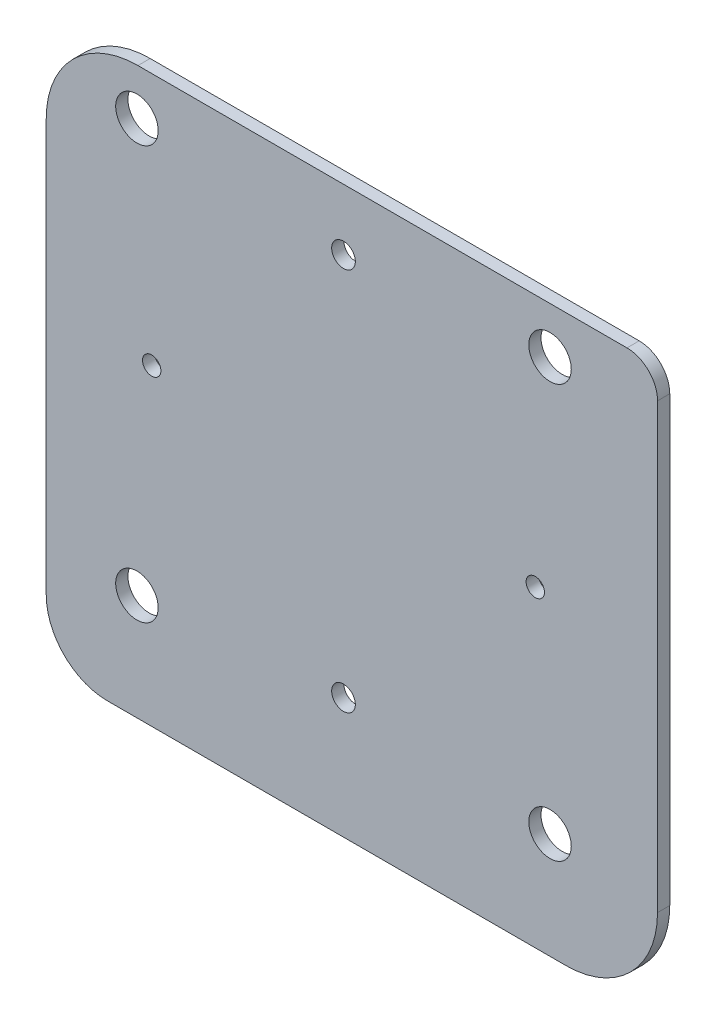
SolidWorks part; units mm, degrees
material "FR4_stuffedProtoboard"
ref_plane "Front Plane" through (0, 0, 0) normal (0, 0, 1) x (1, 0, 0)
ref_plane "Top Plane" through (0, 0, 0) normal (0, 1, 0) x (1, 0, 0)
ref_plane "Right Plane" through (0, 0, 0) normal (1, 0, 0) x (0, 0, -1)
sketch "Imported DXF" plane through (0, 0, 0) normal (0, 0, 1) x (1, 0, 0)
  line L0 (-21.6929, 33.1) -> (40.8929, 33.1)
  line L1 (41.2464, 32.9535) -> (43.9536, 30.2464)
  line L2 (44.1, 29.8929) -> (44.1, -26.6929)
  line L3 (43.9535, -27.0465) -> (30.2464, -40.7536)
  line L4 (29.8929, -40.9) -> (-30.6929, -40.9)
  line L5 (-31.0465, -40.7536) -> (-38.7536, -33.0464)
  line L6 (-38.9001, -32.6946) -> (-38.9148, 15.8797)
  line L7 (-38.7685, 16.2316) -> (-22.0464, 32.9536)
  line L8 (34.175, 6.26) -> (32.925, 6.26)
  line L9 (32.925, 6.26) -> (32.925, 8.26)
  line L10 (32.925, 8.26) -> (34.175, 8.26)
  line L11 (34.175, 8.26) -> (34.175, 6.26)
  line L12 (5.75, 8.485) -> (5.75, 9.735)
  line L13 (5.75, 9.735) -> (7.75, 9.735)
  line L14 (7.75, 9.735) -> (7.75, 8.485)
  line L15 (7.75, 8.485) -> (5.75, 8.485)
  line L16 (-4.91, -8.495) -> (-4.91, -9.745)
  line L17 (-4.91, -9.745) -> (-6.91, -9.745)
  line L18 (-6.91, -9.745) -> (-6.91, -8.495)
  line L19 (-6.91, -8.495) -> (-4.91, -8.495)
  line L20 (39.91, -3.075) -> (32.29, -3.075)
  line L21 (32.29, 3.275) -> (39.91, 3.275)
  line L22 (32.671, -3.075) -> (32.29, -3.075)
  line L23 (32.29, -3.075) -> (32.29, 3.275)
  line L24 (32.29, 3.275) -> (32.671, 3.275)
  line L25 (39.529, -3.075) -> (39.91, -3.075)
  line L26 (39.91, -3.075) -> (39.91, 3.275)
  line L27 (39.91, 3.275) -> (39.529, 3.275)
  line L28 (-3.81, 15.275) -> (3.81, 15.275)
  line L29 (3.81, 8.925) -> (-3.81, 8.925)
  line L30 (3.429, 15.275) -> (3.81, 15.275)
  line L31 (3.81, 15.275) -> (3.81, 8.925)
  line L32 (3.81, 8.925) -> (3.429, 8.925)
  line L33 (-3.429, 15.275) -> (-3.81, 15.275)
  line L34 (-3.81, 15.275) -> (-3.81, 8.925)
  line L35 (-3.81, 8.925) -> (-3.429, 8.925)
  line L36 (3.81, -15.275) -> (-3.81, -15.275)
  line L37 (-3.81, -8.925) -> (3.81, -8.925)
  line L38 (-3.429, -15.275) -> (-3.81, -15.275)
  line L39 (-3.81, -15.275) -> (-3.81, -8.925)
  line L40 (-3.81, -8.925) -> (-3.429, -8.925)
  line L41 (3.429, -15.275) -> (3.81, -15.275)
  line L42 (3.81, -15.275) -> (3.81, -8.925)
  line L43 (3.81, -8.925) -> (3.429, -8.925)
  line L44 (0, 37.7984) -> (0, -46.2816) construction
  line L45 (-65.7891, 0) -> (80.4964, 0) construction
  arc A0 (41.2464, 32.9535) -> (40.8929, 33.1) centre (40.8929, 32.6) ccw
  arc A1 (44.1, 29.8929) -> (43.9535, 30.2464) centre (43.6, 29.8929) ccw
  arc A2 (43.9535, -27.0465) -> (44.1, -26.6929) centre (43.6, -26.6929) ccw
  arc A3 (29.8929, -40.9) -> (30.2464, -40.7536) centre (29.8929, -40.4) ccw
  arc A4 (-31.0465, -40.7536) -> (-30.6929, -40.9) centre (-30.6929, -40.4) ccw
  arc A5 (-38.9001, -32.6946) -> (-38.7537, -33.0464) centre (-38.4001, -32.6928) ccw
  arc A6 (-38.7685, 16.2316) -> (-38.9149, 15.8796) centre (-38.4155, 15.8783) ccw
  arc A7 (-21.6929, 33.1) -> (-22.0465, 32.9535) centre (-21.6929, 32.6) ccw
  circle A8 centre (-25.1, 0) radius 1.2
  circle A9 centre (25.1, 0) radius 1.2
  circle A10 centre (0, 25.1) radius 1.55
  circle A11 centre (0, -25.1) radius 1.55
  circle A12 centre (40.481, 2.989) radius 0.254
  circle A13 centre (-4.381, 9.211) radius 0.254
  circle A14 centre (4.381, -9.211) radius 0.254
  point P20 (0, 0)
  point P40 (33.55, 7.26)
  point P45 (6.75, 9.11)
  point P50 (-5.91, -9.12)
  point P55 (38.1, 26.1)
  point P56 (23.4, 23.4)
  point P57 (-23.4, 23.4)
  point P58 (-23.4, -23.4)
  point P59 (23.4, -23.4)
  point P60 (36.1, 0.1)
  point P71 (0, 12.1)
  point P82 (0, -12.1)
  dimension "D1" = 3.1
sketch "New Imported DXF" plane through (0, 0, 0) normal (0, 0, 1) x (1, 0, 0)
  line L0 (41.1, 29.1) -> (41.1, -28.9)
  line L1 (29.1, -40.9) -> (-30.9, -40.9)
  line L2 (-38.9, -32.9) -> (-38.9, 21.1)
  line L3 (-26.9, 33.1) -> (37.1, 33.1)
  line L4 (-27, -27) -> (27, 27) construction
  line L5 (27, -27) -> (-27, 27) construction
  line L6 (-25.1, 0) -> (25.1, 0) construction
  line L7 (0, 25.1) -> (0, -25.1) construction
  arc A0 (41.1, 29.1) -> (37.1, 33.1) centre (37.1, 29.1) ccw
  arc A1 (29.1, -40.9) -> (41.1, -28.9) centre (29.1, -28.9) ccw
  arc A2 (-38.9, -32.9) -> (-30.9, -40.9) centre (-30.9, -32.9) ccw
  arc A3 (-26.9, 33.1) -> (-38.9, 21.1) centre (-26.9, 21.1) ccw
  circle A4 centre (-25.1, 0) radius 1.2
  circle A5 centre (25.1, 0) radius 1.2
  circle A6 centre (0, 25.1) radius 1.55
  circle A7 centre (0, -25.1) radius 1.55
  circle A8 centre (27, 27) radius 2.75
  circle A9 centre (-27, 27) radius 2.75
  circle A10 centre (27, -27) radius 2.75
  circle A11 centre (-27, -27) radius 2.75
  point P28 (0, 0)
  point P29 (0, 0)
  point P30 (0, 0)
  point P31 (0, 0)
  point P32 (0, 0)
  point P33 (0, 0)
  point P34 (0, 0)
  point P35 (156.5756, 90.538)
  point P36 (0, 0)
  point P37 (0, 0)
  point P39 (0, 0)
  point P40 (0, -4.2416)
  point P41 (0, -25.1)
  dimension "D5" = 4
  dimension "D6" = 12
  dimension "D7" = 8
  dimension "D8" = 12
  dimension "D13" = 5.5
  dimension "D20" = 2.4
  dimension "D21" = 3.1
  dimension "D1" = 54
  dimension "D2" = 58
  dimension "D3" = 64
  dimension "D4" = 60
  dimension "D9" = 38.9
  dimension "D10" = 41.1
  dimension "D11" = 40.9
  dimension "D12" = 33.1
  dimension "D14" = 27
  dimension "D15" = 27
  dimension "D16" = 27
  dimension "D17" = 27
  dimension "D18" = 13.8
sketch "Outline" plane through (0, 0, 0) normal (0, 0, 1) x (1, 0, 0)
  line L9 (-38.9, 21.1) -> (-38.9, -32.9)
  line L10 (-30.9, -40.9) -> (29.1, -40.9)
  line L11 (41.1, -28.9) -> (41.1, 29.1)
  line L12 (-26.9, 33.1) -> (37.1, 33.1) construction
  line L17 (-26.9, 33.1) -> (37.1, 33.1)
  arc A0 (-38.9, 21.1) -> (-26.9, 33.1) centre (-26.9, 21.1) cw
  arc A1 (-26.9, 33.1) -> (-38.9, 21.1) centre (-26.9, 21.1) ccw construction
  arc A2 (41.1, 29.1) -> (37.1, 33.1) centre (37.1, 29.1) ccw
  arc A4 (41.1, -28.9) -> (29.1, -40.9) centre (29.1, -28.9) cw
  arc A5 (-38.9, -32.9) -> (-30.9, -40.9) centre (-30.9, -32.9) ccw
  arc A6 (-38.9, -32.9) -> (-30.9, -40.9) centre (-30.9, -32.9) ccw construction
  arc A7 (41.1, 29.1) -> (37.1, 33.1) centre (37.1, 29.1) ccw construction
extrude "Boss-Extrude1" add sketch "Outline" along normal blind 1.6
sketch "Connector locations" plane through (0, 0, 1.6) normal (0, 0, 1) x (1, 0, 0)
  line L1 (24.5314, 22.2686) -> (22.2686, 24.5314)
  line L2 (38.1, 27.7) -> (38.1, 24.5)
  line L3 (22.2686, -24.5314) -> (24.5314, -22.2686)
  line L4 (0, 0) -> (23.4, 23.4) construction
  line L5 (-24.5314, -22.2686) -> (-22.2686, -24.5314)
  line L6 (-22.2686, 24.5314) -> (-24.5314, 22.2686)
  line L9 (-21.6929, 33.1) -> (40.8929, 33.1) construction
  line L10 (-65.7891, 0) -> (80.4964, 0) construction
  point P13 (38.1, 26.1)
  dimension "D1" = 45
  dimension "D3" = 45
  dimension "D4" = 33.0926
  dimension "D6" = 3.2
sketch "Sketch3" plane through (0, 0, 1.6) normal (0, 0, 1) x (1, 0, 0)
  circle A0 centre (0, 25.1) radius 1.55
  circle A1 centre (25.1, 0) radius 1.2
  circle A2 centre (0, -25.1) radius 1.55
  circle A3 centre (-25.1, 0) radius 1.2
  circle A4 centre (25.1, 0) radius 1.2 construction
  circle A5 centre (0, 25.1) radius 1.55 construction
  circle A6 centre (-25.1, 0) radius 1.2 construction
  circle A7 centre (0, -25.1) radius 1.55 construction
extrude "Cut-Extrude3" cut sketch "Sketch3" against normal up to next
sketch "Press Fit Nut Locations" plane through (0, 0, 1.6) normal (0, 0, 1) x (1, 0, 0)
  circle A0 centre (-27.0307, 27.0307) radius 2.78 construction
  circle A1 centre (27.0307, 27.0307) radius 2.78 construction
  circle A2 centre (-27.0307, -27.0307) radius 2.78 construction
  circle A3 centre (27.0307, -27.0307) radius 2.78 construction
  circle A4 centre (-27.0307, 27.0307) radius 2.78
  circle A5 centre (27.0307, 27.0307) radius 2.78
  circle A6 centre (-27.0307, -27.0307) radius 2.78
  circle A7 centre (27.0307, -27.0307) radius 2.78
sketch "Frame Boss Lines" plane through (0, 0, 1.6) normal (0, 0, 1) x (1, 0, 0)
  line L0 (-41.5, 37.8828) -> (-41.5, -46.4929)
  line L1 (-41.5, -37) -> (-41.5, -41.5) construction
  line L2 (41.5, -37) -> (41.5, -41.5) construction
  line L3 (-41.5, -37) -> (-41.5, -41.5) construction
  line L4 (41.5, -37) -> (41.5, -41.5) construction
  line L7 (41.5, 37.8828) -> (41.5, -46.4929)
extrude "Cut-Extrude4" cut sketch "Press Fit Nut Locations" against normal up to next
